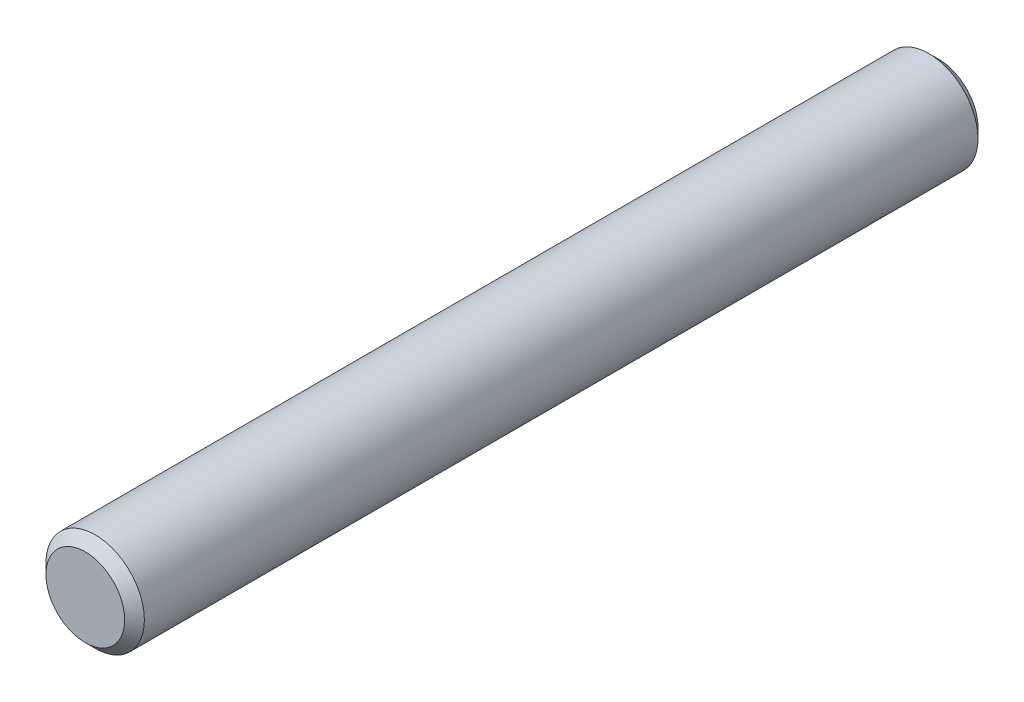
SolidWorks part; units mm, degrees
ref_plane "Front Plane" through (0, 0, 0) normal (0, 0, 1) x (1, 0, 0)
ref_plane "Top Plane" through (0, 0, 0) normal (0, 1, 0) x (1, 0, 0)
ref_plane "Right Plane" through (0, 0, 0) normal (1, 0, 0) x (0, 0, -1)
sketch "Sketch1" plane through (0, 0, 0) normal (0, 0, 1) x (1, 0, 0)
  circle A0 centre (0, 0) radius 1.5
  dimension "D1" = 3
extrude "Boss-Extrude1" add sketch "Sketch1" along normal mid plane 26
chamfer "Chamfer1" distance 0.3 angle 45 2 edges at (1.5, 0, -13) (1.5, 0, 13)
